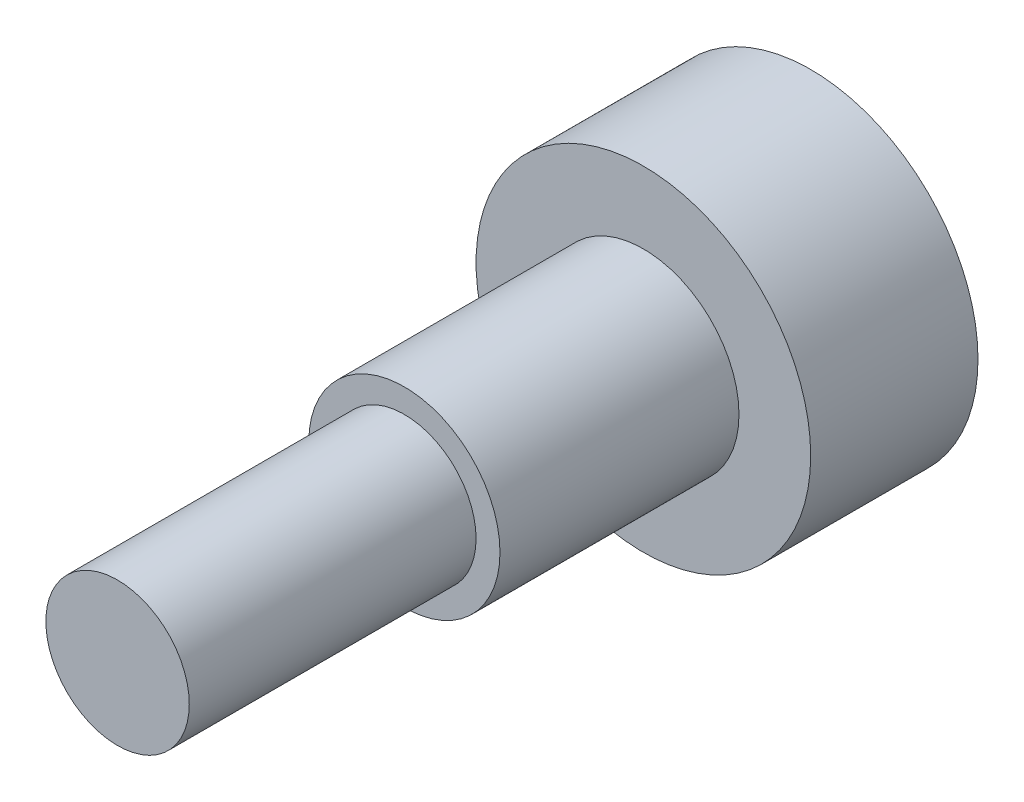
SolidWorks part; units mm, degrees
ref_plane "前视基准面" through (0, 0, 0) normal (0, 0, 1) x (1, 0, 0)
ref_plane "上视基准面" through (0, 0, 0) normal (0, 1, 0) x (1, 0, 0)
ref_plane "右视基准面" through (0, 0, 0) normal (1, 0, 0) x (0, 0, -1)
sketch "草图1" plane through (0, 0, 0) normal (0, 0, 1) x (1, 0, 0)
  circle A0 centre (0, 0) radius 3.5
  point P3 (0, 0)
  dimension "D1" = 7
extrude "凸台-拉伸1" add sketch "草图1" along normal blind 3.5
sketch "草图2" plane through (0, 0, 3.5) normal (0, 0, 1) x (1, 0, 0)
  circle A0 centre (0, 0) radius 2
  dimension "D1" = 4
extrude "凸台-拉伸2" add sketch "草图2" along normal blind 5
sketch "草图3" plane through (0, 0, 8.5) normal (0, 0, 1) x (1, 0, 0)
  circle A0 centre (0, 0) radius 1.5
  dimension "D1" = 3
extrude "凸台-拉伸3" add sketch "草图3" along normal blind 6
